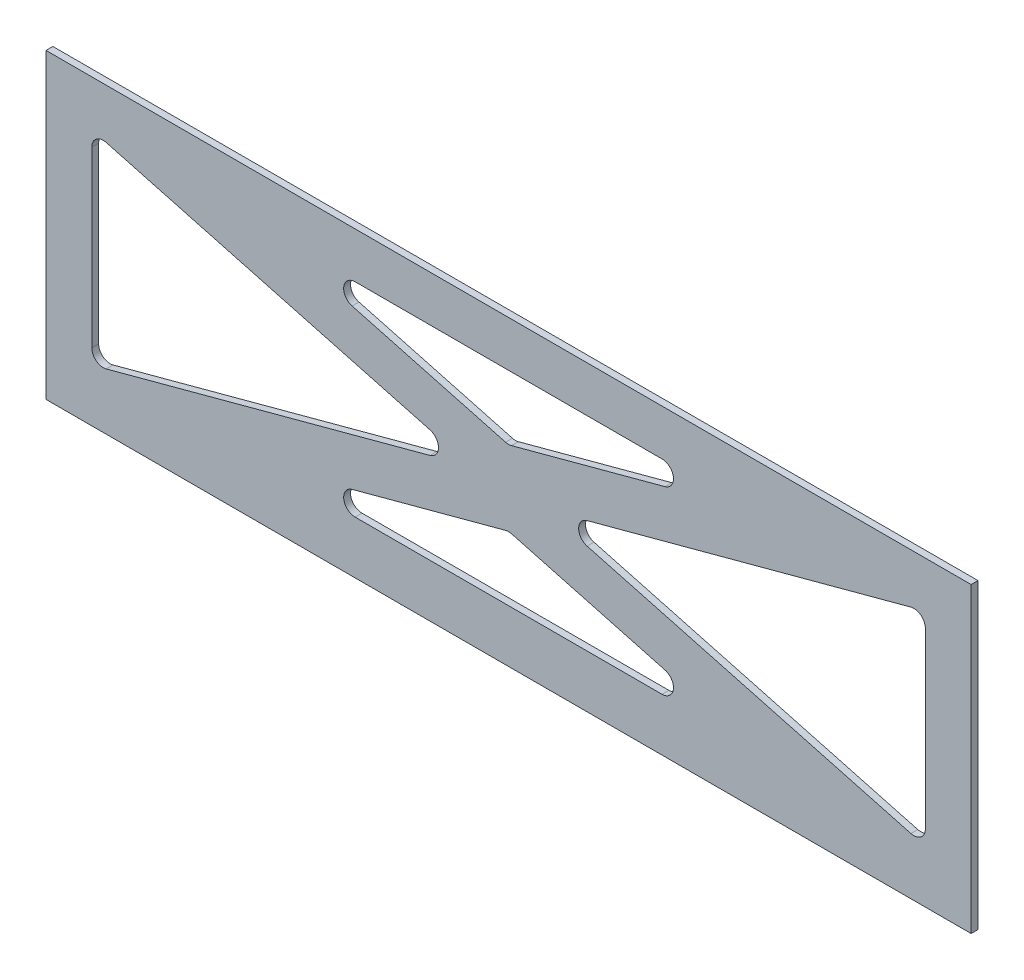
SolidWorks part; units mm, degrees
material "birch 3mm plywood"
ref_plane "Front Plane" through (0, 0, 0) normal (0, 0, 1) x (1, 0, 0)
ref_plane "Top Plane" through (0, 0, 0) normal (0, 1, 0) x (1, 0, 0)
ref_plane "Right Plane" through (0, 0, 0) normal (1, 0, 0) x (0, 0, -1)
sketch "Sketch1" plane through (0, 0, 152) normal (0, 0, 1) x (1, 0, 0)
  line L1 (-116.4734, -3.4092) -> (287.5266, -3.4092)
  line L2 (-116.4734, -3.4092) -> (-116.4734, -135.4092)
  line L3 (-116.4734, -135.4092) -> (287.5266, -135.4092)
  line L4 (287.5266, -3.4092) -> (287.5266, -135.4092)
  line L6 (-96.4734, -105.889) -> (-96.4734, -29.9294)
  line L7 (-90.1764, -25.1006) -> (51.2243, -63.0804)
  line L8 (185.5266, -5.4092) -> (-114.4734, -5.4092) construction
  line L9 (-114.4734, -130.4092) -> (-114.4734, -5.4092) construction
  line L10 (185.5266, -130.4092) -> (-114.4734, -130.4092) construction
  line L12 (285.5266, -130.4092) -> (-114.4734, -130.4092) construction
  line L13 (285.5266, -5.4092) -> (285.5266, -130.4092) construction
  line L14 (-114.4734, -130.4092) -> (-114.4734, -5.4092) construction
  line L15 (-114.4734, -5.4092) -> (285.5266, -5.4092) construction
  line L18 (152.5361, -23.4092) -> (18.5171, -23.4092)
  line L19 (51.2243, -72.738) -> (-90.1764, -110.7178)
  line L20 (17.2201, -33.238) -> (84.2296, -51.2366)
  line L21 (86.8236, -51.2366) -> (153.8331, -33.238)
  line L22 (285.5266, -107.9092) -> (285.5266, -27.9092) construction
  line L23 (261.2296, -25.1006) -> (119.8289, -63.0804)
  line L24 (267.5266, -105.889) -> (267.5266, -29.9294)
  line L25 (119.8289, -72.738) -> (261.2296, -110.7178)
  line L26 (-114.4734, -67.9092) -> (285.5266, -67.9092) construction
  line L27 (17.2201, -102.5804) -> (84.2296, -84.5818)
  line L28 (152.5361, -112.4092) -> (18.5171, -112.4092)
  line L29 (86.8236, -84.5818) -> (153.8331, -102.5804)
  line L30 (85.5266, -51.585) -> (85.5266, -84.2334) construction
  line L31 (69.2023, -67.9092) -> (101.8508, -67.9092) construction
  line L32 (85.5266, -51.585) -> (85.5266, -84.2334) construction
  arc A0 (-90.1764, -110.7178) -> (-96.4734, -105.889) centre (-91.4734, -105.889) cw
  arc A1 (51.2243, -72.738) -> (51.2243, -63.0804) centre (49.9273, -67.9092) ccw
  arc A2 (-90.1764, -25.1006) -> (-96.4734, -29.9294) centre (-91.4734, -29.9294) ccw
  arc A3 (153.8331, -102.5804) -> (152.5361, -112.4092) centre (152.5361, -107.4092) cw
  arc A4 (17.2201, -102.5804) -> (18.5171, -112.4092) centre (18.5171, -107.4092) ccw
  arc A5 (84.2296, -84.5818) -> (86.8236, -84.5818) centre (85.5266, -89.4107) cw
  arc A6 (119.8289, -63.0804) -> (119.8289, -72.738) centre (121.1259, -67.9092) ccw
  arc A7 (261.2296, -110.7178) -> (267.5266, -105.889) centre (262.5266, -105.889) ccw
  arc A8 (267.5266, -29.9294) -> (261.2296, -25.1006) centre (262.5266, -29.9294) ccw
  arc A9 (17.2201, -33.238) -> (18.5171, -23.4092) centre (18.5171, -28.4092) cw
  arc A10 (153.8331, -33.238) -> (152.5361, -23.4092) centre (152.5361, -28.4092) ccw
  arc A11 (86.8236, -51.2366) -> (84.2296, -51.2366) centre (85.5266, -46.4077) cw
  point P14 (85.5266, -67.9092)
  point P15 (85.5266, -67.9092)
  point P32 (-96.4734, -23.4092)
  point P35 (190.4264, -112.4092)
  point P38 (-19.3732, -112.4092)
  point P51 (-19.3732, -23.4092)
  point P54 (190.4264, -23.4092)
  dimension "D9" = 5
  dimension "D10" = 5
  dimension "D1" = 2
  dimension "D2" = 2
  dimension "D3" = 2
  dimension "D4" = 5
  dimension "D5" = 20
  dimension "D6" = 20
  dimension "D7" = 20
  dimension "D8" = 20
  dimension "D11" = 20
extrude "Boss-Extrude1" add sketch "Sketch1" along normal blind 3
